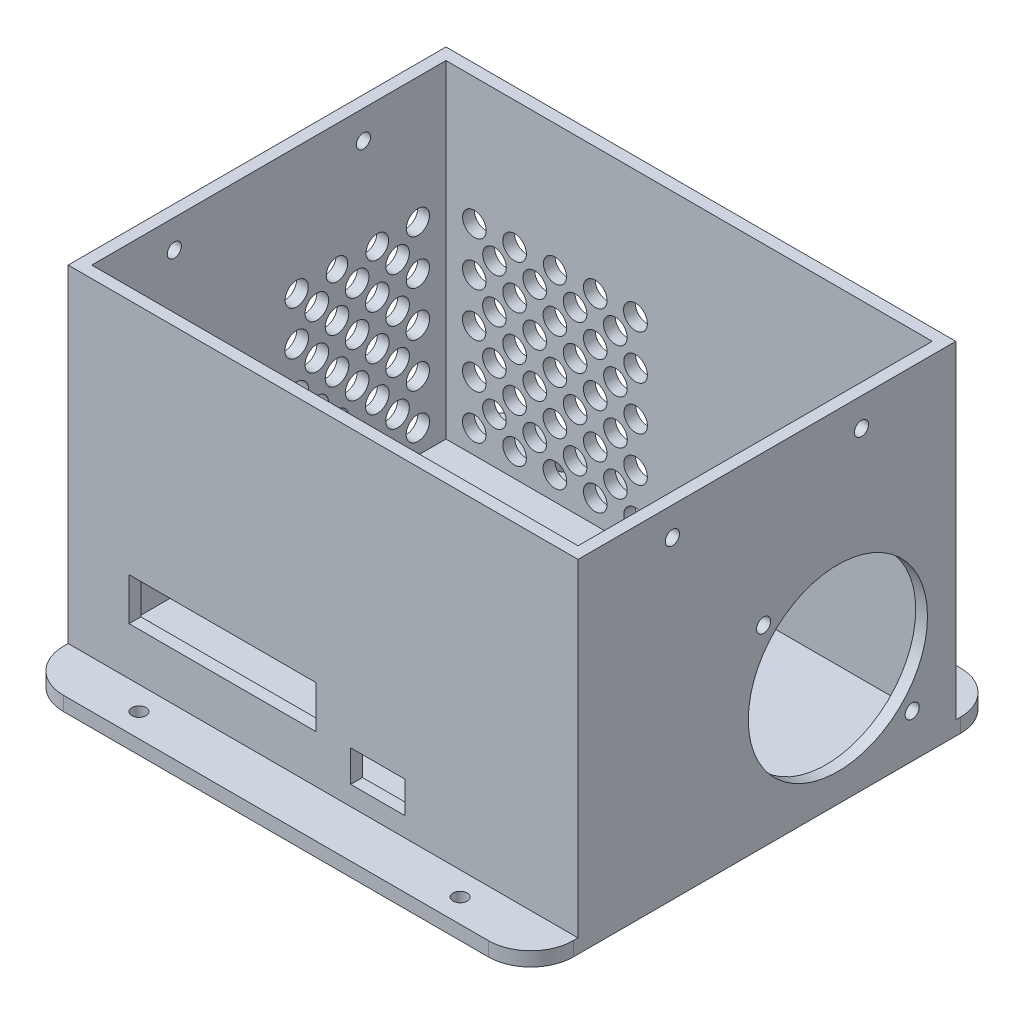
SolidWorks part; units mm, degrees
ref_plane "Front Plane" through (0, 0, 0) normal (0, 0, 1) x (1, 0, 0)
ref_plane "Top Plane" through (0, 0, 0) normal (0, 1, 0) x (1, 0, 0)
ref_plane "Right Plane" through (0, 0, 0) normal (1, 0, 0) x (0, 0, -1)
sketch "Sketch1" plane through (0, 0, 0) normal (0, 1, 0) x (1, 0, 0)
  line L1 (-39.05, -27.95) -> (39.05, -27.95)
  line L2 (-39.05, -27.95) -> (-39.05, 27.95)
  line L3 (-39.05, 27.95) -> (39.05, 27.95)
  line L4 (39.05, -27.95) -> (39.05, 27.95)
  line L5 (-39.05, -27.95) -> (39.05, 27.95) construction
  line L6 (-39.05, 27.95) -> (39.05, -27.95) construction
  point P0 (0, 0)
extrude "Boss-Extrude1" add sketch "Sketch1" along normal blind 3
sketch "Sketch2" plane through (0, 3, 0) normal (0, 1, 0) x (1, 0, 0)
  circle A0 centre (-35.9, 20.9) radius 1.25
  circle A1 centre (-35.9, -24.8) radius 1.25
  circle A2 centre (35.9, -24.8) radius 1.25
  circle A3 centre (35.9, 24.8) radius 1.25
extrude "Cut-Extrude1" cut sketch "Sketch2" against normal blind 68
sketch "Sketch3" plane through (0, 3, 0) normal (0, 1, 0) x (1, 0, 0)
  line L0 (-39.05, -27.95) -> (39.05, -27.95) construction
  line L5 (-31.15, -27.95) -> (8.45, -27.95)
  line L6 (-31.15, -27.95) -> (-31.15, -12.75)
  line L7 (-31.15, -12.75) -> (8.45, -12.75)
  line L8 (8.45, -27.95) -> (8.45, -12.75)
  line L13 (27.35, -17.65) -> (15.85, -17.65)
  line L14 (27.35, -17.65) -> (27.35, -27.95)
  line L15 (27.35, -27.95) -> (15.85, -27.95)
  line L16 (15.85, -17.65) -> (15.85, -27.95)
  line L18 (-39.05, 27.95) -> (39.05, 27.95)
  line L19 (-39.05, 27.95) -> (-39.05, -27.95)
  line L20 (-39.05, -27.95) -> (39.05, -27.95)
  line L21 (39.05, 27.95) -> (39.05, -27.95)
  circle A0 centre (35.9, 24.8) radius 1.25
  circle A1 centre (35.9, -24.8) radius 1.25
  circle A2 centre (-35.9, -24.8) radius 1.25
  circle A3 centre (-35.9, 20.9) radius 1.25
sketch "Sketch4" plane through (0, 0, 0) normal (0, -1, 0) x (-1, 0, 0)
  line L0 (0, -27.95) -> (0, -29.95) construction
  line L1 (39.05, 27.95) -> (-39.05, 27.95)
  line L2 (39.05, 27.95) -> (39.05, -27.95)
  line L3 (39.05, -27.95) -> (-39.05, -27.95)
  line L4 (-39.05, 27.95) -> (-39.05, -27.95)
  line L5 (39.05, 27.95) -> (-39.05, -27.95) construction
  line L6 (39.05, -27.95) -> (-39.05, 27.95) construction
  line L7 (41.05, 29.95) -> (-41.05, 29.95)
  line L8 (41.05, 29.95) -> (41.05, -29.95)
  line L9 (41.05, -29.95) -> (-41.05, -29.95)
  line L10 (-41.05, 29.95) -> (-41.05, -29.95)
  line L11 (41.05, 29.95) -> (-41.05, -29.95) construction
  line L12 (41.05, -29.95) -> (-41.05, 29.95) construction
  line L13 (-39.05, 0) -> (-41.05, 0) construction
  point P0 (0, 0)
  point P7 (0, 0)
extrude "Boss-Extrude3" add sketch "Sketch4" against normal blind 3
sketch "Sketch6" plane through (0, 3, 0) normal (0, 1, 0) x (1, 0, 0)
  circle A0 centre (-35.9, -24.8) radius 1.25
  circle A1 centre (35.9, -24.8) radius 1.25
  circle A2 centre (35.9, 24.8) radius 1.25
  circle A3 centre (-35.9, 20.9) radius 1.25
  circle A4 centre (-35.9, 20.9) radius 3
  circle A5 centre (35.9, 24.8) radius 3
  circle A6 centre (35.9, -24.8) radius 3
  circle A7 centre (-35.9, -24.8) radius 3
extrude "Boss-Extrude4" add sketch "Sketch6" along normal blind 3.5
sketch "Sketch7" plane through (0, 0, 0) normal (0, -1, 0) x (-1, 0, 0)
  line L1 (-41.05, 29.95) -> (41.05, 29.95)
  line L2 (-41.05, 29.95) -> (-41.05, 46.15)
  line L3 (-41.05, 46.15) -> (41.05, 46.15)
  line L4 (41.05, 29.95) -> (41.05, 46.15)
extrude "Boss-Extrude5" add sketch "Sketch7" against normal blind 3
sketch "Sketch8" plane through (0, 0, -46.15) normal (0, 0, -1) x (-1, 0, 0)
  line L1 (-41.05, 0) -> (41.05, 0)
  line L2 (-41.05, 0) -> (-41.05, 50.5)
  line L3 (-41.05, 50.5) -> (41.05, 50.5)
  line L4 (41.05, 0) -> (41.05, 50.5)
extrude "Boss-Extrude6" add sketch "Sketch8" along normal blind 3
sketch "Sketch10" plane through (41.05, 0, 0) normal (1, 0, 0) x (0, 0, -1)
  line L1 (46.15, 50.5) -> (49.15, 50.5)
  line L2 (46.15, 50.5) -> (46.15, 0)
  line L3 (46.15, 0) -> (49.15, 0)
  line L4 (49.15, 50.5) -> (49.15, 0)
  line L5 (-29.95, 0) -> (46.15, 0)
  line L6 (-29.95, 0) -> (-29.95, 3)
  line L7 (-29.95, 3) -> (46.15, 3)
  line L8 (46.15, 0) -> (46.15, 3)
  line M1 (-29.95, 0) -> (49.15, 0)
  line M5 (46.15, 3) -> (-29.95, 3)
  line M6 (-29.95, 3) -> (-29.95, 0)
extrude "Boss-Extrude7" add sketch "Sketch10" along normal blind 20 contours L2 M5 M6 M1
sketch "Sketch12" plane through (-41.05, 0, 0) normal (-1, 0, 0) x (0, 0, 1)
  line L1 (-49.15, 50.5) -> (29.95, 50.5)
  line L2 (-49.15, 50.5) -> (-49.15, 0)
  line L3 (-49.15, 0) -> (29.95, 0)
  line L4 (29.95, 50.5) -> (29.95, 0)
extrude "Boss-Extrude8" add sketch "Sketch12" along normal blind 3
sketch "Sketch17" plane through (0, 0, 29.95) normal (0, 0, 1) x (1, 0, 0)
  line L1 (-44.05, 50.5) -> (61.05, 50.5)
  line L2 (-44.05, 50.5) -> (-44.05, 0)
  line L3 (-44.05, 0) -> (61.05, 0)
  line L4 (61.05, 50.5) -> (61.05, 0)
extrude "Boss-Extrude13" add sketch "Sketch17" against normal blind 2 and the other way blind 1
sketch "Sketch18" plane through (0, 0, 27.95) normal (0, 0, -1) x (-1, 0, 0)
  line L0 (-61.05, 3) -> (-61.05, 50.5) construction
  line L1 (41.05, 3) -> (-61.05, 3)
  line L2 (41.05, 3) -> (41.05, 6.5)
  line L4 (-61.05, 3) -> (-61.05, 6.5)
  line L10 (-8.45, 8.1) -> (-8.45, 13.1) construction
  line L19 (-8.45, 8.1) -> (-8.45, 22.1) construction
  line L21 (-8.45, 22.1) -> (31.15, 22.1)
  line L22 (-8.45, 22.1) -> (-8.45, 13.1)
  line L23 (-8.45, 13.1) -> (31.15, 13.1)
  line L24 (31.15, 22.1) -> (31.15, 13.1)
  line L31 (-25.35, 8.1) -> (-17.85, 11.8) construction
  line L32 (-25.35, 11.8) -> (-17.85, 8.1) construction
  line L38 (-27.35, 6.1) -> (-15.85, 6.1)
  line L39 (-27.35, 6.1) -> (-27.35, 13.8)
  line L40 (-27.35, 13.8) -> (-15.85, 13.8)
  line L41 (-15.85, 6.1) -> (-15.85, 13.8)
  line L42 (-27.35, 6.1) -> (-15.85, 13.8) construction
  line L43 (-27.35, 13.8) -> (-15.85, 6.1) construction
  point P7 (-21.6, 9.95)
  point P8 (-21.6, 9.95)
  point P27 (-21.6, 9.95)
  point P32 (-21.6, 9.95)
extrude "Cut-Extrude4" cut sketch "Sketch18" against normal blind 9 contours L38 L41 L40 L39 | L24 L21 L22 L23
sketch "Sketch19" plane through (61.05, 0, 0) normal (1, 0, 0) x (0, 0, -1)
  line L1 (-30.95, 50.5) -> (49.15, 50.5)
  line L2 (-30.95, 50.5) -> (-30.95, 0)
  line L3 (-30.95, 0) -> (49.15, 0)
  line L4 (49.15, 50.5) -> (49.15, 0)
extrude "Boss-Extrude14" add sketch "Sketch19" along normal blind 3
sketch "Sketch20" plane through (61.05, 0, 0) normal (-1, 0, 0) x (0, 0, 1)
  line L0 (-34.985, 3) -> (-34.985, 5) construction
  line L1 (-46.15, 3) -> (27.95, 3) construction
  line L2 (-46.15, 21.4946) -> (-44.15, 21.4946) construction
  line L3 (-46.15, 50.5) -> (-46.15, 3) construction
  line L4 (-44.15, 45) -> (-4.15, 5) construction
  line L14 (-39.9, 9.25) -> (-8.4, 40.75) construction
  line L15 (-39.9, 40.75) -> (-8.4, 9.25) construction
  circle A0 centre (-24.15, 25) radius 19
  circle A1 centre (-8.4, 40.75) radius 1.5
  circle A2 centre (-39.9, 40.75) radius 1.5
  circle A3 centre (-8.4, 9.25) radius 1.5
  circle A4 centre (-39.9, 9.25) radius 1.5
extrude "Cut-Extrude5" cut sketch "Sketch20" against normal blind 3
sketch "Sketch22" plane through (-41.05, 0, 0) normal (1, 0, 0) x (0, 0, -1)
  line L0 (46.15, 3) -> (27.95, 3) construction
  line L1 (-27.95, 3) -> (46.15, 3) construction
  line L2 (27.95, 3) -> (9.95, 3) construction
  line L3 (46.15, 26.75) -> (44.15, 26.75) construction
  line L4 (46.15, 3) -> (46.15, 50.5) construction
  line L5 (9.95, 45.5) -> (9.95, 36.125) construction
  line L6 (-27.95, 50.5) -> (46.15, 50.5) construction
  line L7 (44.15, 3) -> (44.15, 50.5) construction
  line L8 (18.5, 50.5) -> (18.5, 3) construction
  line L9 (9.95, 50.5) -> (18.5, 50.5) construction
  line L10 (27.05, 50.5) -> (27.05, 3) construction
  line L11 (18.5, 50.5) -> (27.05, 50.5) construction
  line L12 (35.6, 50.5) -> (35.6, 3) construction
  line L13 (27.05, 50.5) -> (35.6, 50.5) construction
  line L14 (35.6, 50.5) -> (44.15, 50.5) construction
  line L15 (14.225, 50.5) -> (14.225, 3) construction
  line L16 (22.775, 50.5) -> (22.775, 3) construction
  line L17 (31.325, 50.5) -> (31.325, 3) construction
  line L18 (39.875, 50.5) -> (39.875, 3) construction
  line L19 (9.95, 26.75) -> (44.15, 26.75) construction
  line L20 (9.95, 36.125) -> (9.95, 26.75) construction
  line L21 (9.95, 45.5) -> (44.15, 45.5) construction
  line L22 (9.95, 8) -> (44.15, 8) construction
  line L23 (9.95, 17.375) -> (44.15, 17.375) construction
  line L24 (9.95, 36.125) -> (44.15, 36.125) construction
  line L25 (9.95, 26.75) -> (9.95, 17.375) construction
  line L26 (9.95, 17.375) -> (9.95, 8) construction
  line L27 (9.95, 40.8125) -> (44.15, 40.8125) construction
  line L28 (9.95, 31.4375) -> (44.15, 31.4375) construction
  line L29 (9.95, 22.0625) -> (44.15, 22.0625) construction
  line L30 (9.95, 12.6875) -> (44.15, 12.6875) construction
  circle A0 centre (14.225, 12.6875) radius 2.5
  circle A1 centre (14.225, 22.0625) radius 2.5
  circle A2 centre (18.5, 17.375) radius 2.5
  circle A3 centre (22.775, 22.0625) radius 2.5
  circle A4 centre (22.775, 12.6875) radius 2.5
  circle A5 centre (14.225, 31.4375) radius 2.5
  circle A6 centre (18.5, 26.75) radius 2.5
  circle A7 centre (22.775, 31.4375) radius 2.5
  circle A8 centre (18.5, 36.125) radius 2.5
  circle A9 centre (14.225, 40.8125) radius 2.5
  circle A10 centre (22.775, 40.8125) radius 2.5
  circle A11 centre (27.05, 36.125) radius 2.5
  circle A12 centre (31.325, 40.8125) radius 2.5
  circle A13 centre (39.875, 40.8125) radius 2.5
  circle A14 centre (35.6, 36.125) radius 2.5
  circle A15 centre (39.875, 31.4375) radius 2.5
  circle A16 centre (31.325, 31.4375) radius 2.5
  circle A17 centre (27.05, 26.75) radius 2.5
  circle A18 centre (31.325, 22.0625) radius 2.5
  circle A19 centre (39.875, 22.0625) radius 2.5
  circle A20 centre (35.6, 26.75) radius 2.5
  circle A21 centre (27.05, 17.375) radius 2.5
  circle A22 centre (31.325, 12.6875) radius 2.5
  circle A23 centre (39.875, 12.6875) radius 2.5
  circle A24 centre (35.6, 17.375) radius 2.5
  circle A26 centre (18.5, 8) radius 2.5
  circle A27 centre (27.05, 8) radius 2.5
  circle A28 centre (35.6, 8) radius 2.5
extrude "Cut-Extrude6" cut sketch "Sketch22" against normal blind 3
sketch "Sketch23" plane through (0, 50.5, 0) normal (0, 1, 0) x (1, 0, 0)
  line L1 (-41.05, -27.95) -> (61.05, -27.95)
  line L2 (-41.05, -27.95) -> (-41.05, 46.15)
  line L3 (-41.05, 46.15) -> (61.05, 46.15)
  line L4 (61.05, -27.95) -> (61.05, 46.15)
  line L5 (64.05, -30.95) -> (-44.05, -30.95)
  line L6 (64.05, -30.95) -> (64.05, 49.15)
  line L7 (64.05, 49.15) -> (-44.05, 49.15)
  line L8 (-44.05, -30.95) -> (-44.05, 49.15)
extrude "Boss-Extrude15" add sketch "Sketch23" along normal blind 22
sketch "Sketch24" plane through (-44.05, 0, 0) normal (-1, 0, 0) x (0, 0, 1)
  circle A0 centre (-29.15, 66.5) radius 1.5
  circle A1 centre (10.95, 66.5) radius 1.5
extrude "Cut-Extrude7" cut sketch "Sketch24" against normal blind 200
sketch "Sketch25" plane through (-44.05, 0, 0) normal (-1, 0, 0) x (0, 0, 1)
  line L0 (-27.05, 36.125) -> (-27.05, 45.5) construction
  line L2 (-35.6, 36.125) -> (-35.6, 26.75)
  line L3 (-35.6, 26.75) -> (-27.05, 26.75)
  line L4 (-27.05, 36.125) -> (-27.05, 26.75)
  line L6 (-18.5, 36.125) -> (-18.5, 26.75)
  line L7 (-18.5, 26.75) -> (-27.05, 26.75)
  line L8 (-27.05, 36.125) -> (-27.05, 26.75)
  line L9 (-35.6, 36.125) -> (-35.6, 45.5) construction
  line L10 (-18.5, 36.125) -> (-18.5, 45.5) construction
  circle A0 centre (-35.6, 45.5) radius 2.5
  circle A1 centre (-27.05, 45.5) radius 2.5
  circle A2 centre (-18.5, 45.5) radius 2.5
extrude "Cut-Extrude9" cut sketch "Sketch25" against normal blind 13.5 contours A0 | A1 | A2
sketch "Sketch26" plane through (0, 72.5, 0) normal (0, 1, 0) x (1, 0, 0)
  line L0 (10, -27.95) -> (10, -28.45) construction
  line L1 (61.05, 46.15) -> (-41.05, -27.95) construction
  line L2 (61.05, 9.1) -> (61.55, 9.1) construction
  line L3 (-41.05, 46.15) -> (61.05, 46.15)
  line L4 (-41.05, 46.15) -> (-41.05, -27.95)
  line L5 (-41.05, -27.95) -> (61.05, -27.95)
  line L6 (61.05, 46.15) -> (61.05, -27.95)
  line L7 (-41.05, 46.15) -> (61.05, -27.95) construction
  line L8 (-41.05, -27.95) -> (61.05, 46.15) construction
  line L10 (-41.55, 46.65) -> (61.55, 46.65)
  line L11 (-41.55, 46.65) -> (-41.55, -28.45)
  line L12 (-41.55, -28.45) -> (61.55, -28.45)
  line L13 (61.55, 46.65) -> (61.55, -28.45)
  line L14 (-41.55, 46.65) -> (61.55, -28.45) construction
  line L15 (-41.55, -28.45) -> (61.55, 46.65) construction
  point P0 (10, 9.1)
  point P12 (10, 9.1)
extrude "Cut-Extrude13" cut sketch "Sketch26" against normal blind 69.5
sketch "Sketch27" plane through (0, 0, 30.95) normal (0, 0, 1) x (1, 0, 0)
  line L0 (27.35, 13.8) -> (27.35, 6.1) construction
  line L1 (15.85, 6.1) -> (27.35, 6.1)
  line L2 (15.85, 6.1) -> (15.85, 7.1)
  line L3 (15.85, 7.1) -> (27.35, 7.1)
  line L4 (27.35, 6.1) -> (27.35, 7.1)
extrude "Boss-Extrude17" add sketch "Sketch27" against normal blind 2.5
sketch "Sketch28" plane through (64.05, 0, 0) normal (1, 0, 0) x (0, 0, -1)
  circle A0 centre (39.9, 40.75) radius 1.5
  circle A1 centre (8.4, 9.25) radius 1.5
extrude "Boss-Extrude18" add sketch "Sketch28" against normal blind 2.5
sketch "Sketch30" plane through (0, 0, -49.15) normal (0, 0, -1) x (-1, 0, 0)
  line L0 (0, 0) -> (0, 5.5) construction
  line L1 (44.05, 36.25) -> (38.05, 36.25) construction
  line L2 (44.05, 72.5) -> (44.05, 0) construction
  line L3 (38.05, 5.5) -> (38.05, 48) construction
  line L4 (38.05, 5.5) -> (35.55, 5.5) construction
  line L5 (35.55, 5.5) -> (35.55, 8) construction
  line L6 (1.377, 45.5246) -> (9.9026, 36.1763) construction
  line L71 (18.45, 45.5484) -> (9.9026, 36.1763) construction
  line L72 (18.45, 45.5484) -> (27, 36.1734) construction
  line L73 (35.5259, 45.522) -> (27, 36.1734) construction
  line L74 (35.5721, 26.7742) -> (27, 36.1734) construction
  line L75 (18.4526, 26.8013) -> (27, 36.1734) construction
  line L76 (18.4526, 26.8013) -> (9.9026, 36.1763) construction
  line L77 (1.3279, 26.7742) -> (9.9026, 36.1763) construction
  line L78 (1.3279, 26.7742) -> (9.889, 17.3871) construction
  line L79 (18.4526, 26.8013) -> (9.889, 17.3871) construction
  line L80 (9.889, 17.3871) -> (1.35, 8) construction
  line L81 (9.889, 17.3871) -> (18.45, 8) construction
  line L82 (18.45, 8) -> (27, 17.375) construction
  line L83 (27, 17.375) -> (35.5721, 26.7742) construction
  line L84 (18.4526, 26.8013) -> (27, 17.375) construction
  line L85 (27, 17.375) -> (35.55, 8) construction
  line L86 (35.55, 5.5) -> (1.35, 5.5) construction
  line L87 (-1.15, 8) -> (-1.15, 49.1983) construction
  line L88 (18.45, 45.5484) -> (18.45, 48) construction
  line L89 (38.05, 48) -> (-6.8735, 48) construction
  circle A0 centre (35.55, 8) radius 2.5
  circle A1 centre (27, 8) radius 2.5
  circle A2 centre (18.45, 8) radius 2.5
  circle A3 centre (9.9, 8) radius 2.5
  circle A4 centre (1.35, 8) radius 2.5
  circle A5 centre (5.6195, 12.6935) radius 2.5
  circle A6 centre (14.1695, 12.6935) radius 2.5
  circle A7 centre (22.725, 12.6875) radius 2.5
  circle A8 centre (31.275, 12.6875) radius 2.5
  circle A9 centre (27, 17.375) radius 2.5
  circle A10 centre (35.55, 17.375) radius 2.5
  circle A11 centre (35.5721, 26.7742) radius 2.4779
  circle A12 centre (35.55, 36.125) radius 2.5031
  circle A13 centre (35.5259, 45.522) radius 2.5
  circle A14 centre (1.35, 17.375) radius 2.5
  circle A15 centre (1.3279, 26.7742) radius 2.4779
  circle A16 centre (1.35, 36.125) radius 2.5
  circle A17 centre (1.377, 45.5246) radius 2.527
  circle A18 centre (18.45, 45.5484) radius 2.4516
  circle A19 centre (9.9, 45.5) radius 2.5
  circle A20 centre (27, 45.5) radius 2.5
  circle A21 centre (27, 36.1734) radius 2.5
  circle A22 centre (18.4526, 36.1763) radius 2.5
  circle A23 centre (9.9026, 36.1763) radius 2.5
  circle A24 centre (9.9026, 26.8013) radius 2.5
  circle A25 centre (18.4526, 26.8013) radius 2.5
  circle A26 centre (27, 26.75) radius 2.5
  circle A27 centre (18.45, 17.375) radius 2.5
  circle A28 centre (9.889, 17.3871) radius 2.5
  circle A29 centre (5.6085, 22.0806) radius 2.5
  circle A30 centre (14.1708, 22.0942) radius 2.5
  circle A31 centre (22.7263, 22.0881) radius 2.5
  circle A32 centre (31.286, 22.0746) radius 2.5
  circle A33 centre (31.286, 31.4738) radius 2.5
  circle A34 centre (31.263, 40.8477) radius 2.5
  circle A35 centre (22.725, 40.8125) radius 2.5
  circle A36 centre (22.7263, 31.4873) radius 2.5
  circle A37 centre (14.1776, 31.4888) radius 2.5
  circle A38 centre (14.1763, 40.8623) radius 2.5
  circle A39 centre (5.6398, 40.8504) radius 2.5
  circle A40 centre (5.6153, 31.4752) radius 2.5
extrude "Cut-Extrude14" cut sketch "Sketch30" against normal blind 2.5
sketch "Sketch32" plane through (-44.05, 0, 0) normal (-1, 0, 0) x (0, 0, 1)
  line L1 (-44.8847, 3.0163) -> (-6.1352, 3.0163)
  line L2 (-44.8847, 3.0163) -> (-44.8847, 54.6136)
  line L3 (-44.8847, 54.6136) -> (-6.1352, 54.6136)
  line L4 (-6.1352, 3.0163) -> (-6.1352, 54.6136)
extrude "Boss-Extrude19" add sketch "Sketch32" against normal blind 2.5
sketch "Sketch33" plane through (-44.05, 0, 0) normal (-1, 0, 0) x (0, 0, 1)
  line L0 (-49.15, 36.25) -> (-43.1454, 36.25) construction
  line L1 (-49.15, 72.5) -> (-49.15, 0) construction
  line L2 (-27.5217, 0) -> (-27.5217, 5.5449) construction
  line L3 (-49.15, 0) -> (30.95, 0) construction
  line L4 (-27.5217, 5.5449) -> (-43.1454, 5.5449) construction
  line L5 (-43.1454, 5.5449) -> (-43.1454, 52.2855) construction
  line L6 (-43.1454, 52.2855) -> (-40.6908, 52.2855) construction
  line L7 (-46.3435, 5.5) -> (-46.3435, 8.027) construction
  line L8 (-43.1454, 8.027) -> (10.4369, 8.027) construction
  line L9 (-40.6908, 52.2855) -> (-40.6908, 8.027) construction
  line L10 (-34.8548, 45.61) -> (-34.8548, 48) construction
  line L27 (-43.1454, 48) -> (11.8441, 48) construction
  line L28 (-40.6908, 8.027) -> (-32.0922, 17.4804) construction
  line L77 (-32.0922, 17.4804) -> (-23.5442, 8.027) construction
  line L78 (-14.9971, 17.4238) -> (-23.5442, 8.027) construction
  line L79 (-14.9971, 17.4238) -> (-6.5002, 8.027) construction
  line L80 (-14.9971, 17.4238) -> (-6.4519, 26.8185) construction
  line L81 (-14.999, 36.2708) -> (-6.4519, 26.8185) construction
  line L82 (-14.999, 36.2708) -> (-6.5119, 45.6016) construction
  line L83 (-23.5451, 45.7222) -> (-14.999, 36.2708) construction
  line L84 (-14.999, 36.2708) -> (-23.5442, 26.8761) construction
  line L85 (-14.9971, 17.4238) -> (-23.5442, 26.8761) construction
  line L87 (-23.5442, 26.8761) -> (-32.0922, 17.4804) construction
  line L88 (-32.0922, 17.4804) -> (-40.6908, 26.8761) construction
  line L89 (-32.0922, 36.3274) -> (-40.6908, 26.8761) construction
  line L90 (-40.6908, 26.8761) -> (-32.0922, 36.3274) construction
  line L91 (-23.5442, 26.8761) -> (-32.0922, 36.3274) construction
  line L92 (-23.5451, 45.7222) -> (-32.0922, 36.3274) construction
  line L93 (-40.6908, 45.8347) -> (-32.0922, 36.3274) construction
  line L94 (-6.4519, 26.8185) -> (-3.95, 26.8185) construction
  line L95 (-3.95, 48) -> (-3.95, 8.027) construction
  circle A0 centre (-40.6908, 8.027) radius 2.4821
  circle A1 centre (-40.6908, 17.4804) radius 2.4545
  circle A2 centre (-40.6908, 26.8761) radius 2.5
  circle A3 centre (-40.6908, 36.3274) radius 2.4558
  circle A4 centre (-40.6908, 45.8347) radius 2.4545
  circle A5 centre (-32.096, 45.61) radius 2.39
  circle A6 centre (-23.5451, 45.7222) radius 2.2778
  circle A7 centre (-15.0019, 45.548) radius 2.452
  circle A8 centre (-36.3915, 41.0811) radius 2.5
  circle A9 centre (-27.8187, 41.0248) radius 2.5
  circle A10 centre (-19.272, 40.9965) radius 2.5
  circle A11 centre (-14.999, 36.2708) radius 2.5
  circle A12 centre (-14.9999, 26.8185) radius 2.5
  circle A13 centre (-14.9971, 17.4238) radius 2.5
  circle A14 centre (-14.9999, 8.027) radius 2.5
  circle A15 centre (-23.5442, 8.027) radius 2.5
  circle A16 centre (-32.0922, 8.027) radius 2.4821
  circle A17 centre (-32.0922, 17.4804) radius 2.5
  circle A18 centre (-32.0922, 26.8761) radius 2.5
  circle A19 centre (-23.5442, 26.8761) radius 2.5
  circle A20 centre (-23.5442, 17.4804) radius 2.5
  circle A21 centre (-36.3915, 31.6018) radius 2.5
  circle A22 centre (-27.8182, 31.6018) radius 2.5
  circle A23 centre (-23.5442, 36.3274) radius 2.5
  circle A24 centre (-19.2716, 31.5735) radius 2.5
  circle A27 centre (-27.8182, 22.1783) radius 2.5
  circle A28 centre (-36.3915, 22.1783) radius 2.5
  circle A29 centre (-36.375, 12.6875) radius 2.5
  circle A30 centre (-27.8182, 12.7537) radius 2.5
  circle A31 centre (-19.2706, 12.7254) radius 2.5
  circle A32 centre (-19.2706, 22.15) radius 2.5
  circle A33 centre (-32.0922, 36.3274) radius 2.5
extrude "Cut-Extrude15" cut sketch "Sketch33" against normal blind 2.5
sketch "Sketch34" plane through (0, 0, 30.95) normal (0, 0, 1) x (1, 0, 0)
  line L0 (64.05, 72.5) -> (64.05, 0) construction
  line L1 (-44.05, 0) -> (64.05, 0)
  line L2 (-44.05, 0) -> (-44.05, 3)
  line L3 (-44.05, 3) -> (64.05, 3)
  line L4 (64.05, 0) -> (64.05, 3)
extrude "Boss-Extrude20" add sketch "Sketch34" along normal blind 10
sketch "Sketch35" plane through (0, 0, -49.15) normal (0, 0, -1) x (-1, 0, 0)
  line L0 (44.05, 72.5) -> (44.05, 0) construction
  line L1 (-64.05, 0) -> (44.05, 0)
  line L2 (-64.05, 0) -> (-64.05, 3)
  line L3 (-64.05, 3) -> (44.05, 3)
  line L4 (44.05, 0) -> (44.05, 3)
extrude "Boss-Extrude21" add sketch "Sketch35" along normal blind 10
sketch "Sketch36" plane through (0, 3, 0) normal (0, 1, 0) x (1, 0, 0)
  line L0 (64.05, 54.15) -> (44.05, 54.15) construction
  line L1 (64.05, 59.15) -> (64.05, 49.15) construction
  line L2 (-44.05, 54.15) -> (-24.05, 54.15) construction
  line L3 (-44.05, 59.15) -> (-44.05, 49.15) construction
  line L4 (-44.05, -35.95) -> (-24.05, -35.95) construction
  line L5 (-44.05, -40.95) -> (-44.05, -30.95) construction
  line L6 (64.05, -35.95) -> (44.05, -35.95) construction
  line L7 (64.05, -40.95) -> (64.05, -30.95) construction
  circle A0 centre (44.05, 54.15) radius 1.5
  circle A1 centre (-24.05, 54.15) radius 1.5
  circle A2 centre (44.05, -35.95) radius 1.5
  circle A3 centre (-24.05, -35.95) radius 1.5
extrude "Cut-Extrude16" cut sketch "Sketch36" against normal blind 10
fillet "Fillet2" radius 9 4 edges at (64.05, 1.5, -59.15) (64.05, 1.5, 40.95) (-44.05, 1.5, -59.15) (-44.05, 1.5, 40.95)
